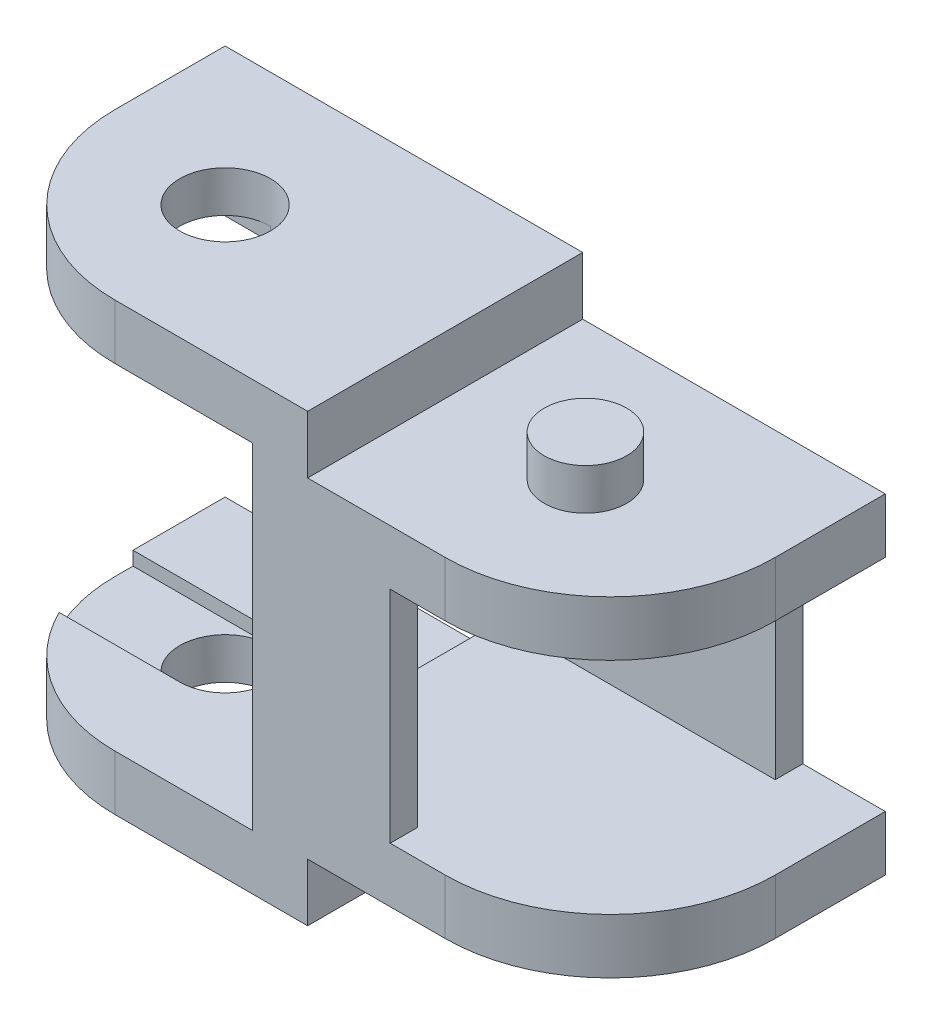
SolidWorks part; units mm, degrees
material "Сталь 45 ГОСТ 1050-2013"
ref_plane "Спереди" through (0, 0, 0) normal (0, 0, 1) x (1, 0, 0)
ref_plane "Сверху" through (0, 0, 0) normal (0, 1, 0) x (1, 0, 0)
ref_plane "Справа" through (0, 0, 0) normal (1, 0, 0) x (0, 0, -1)
sketch "Эскиз2" plane through (0, 0, 0) normal (0, 0, 1) x (1, 0, 0)
  line L0 (0, 0) -> (0, 2)
  line L1 (0, 2) -> (13, 2)
  line L2 (13, 2) -> (13, -0.1)
  line L3 (13, -0.1) -> (24, -0.1)
  line L4 (24, -0.1) -> (24, -2.1)
  line L5 (24, -2.1) -> (11, -2.1)
  line L6 (11, -2.1) -> (11, 0)
  line L7 (11, 0) -> (0, 0)
  point P3 (11, -2.0413)
  point P10 (0, 0)
  point P11 (0, 0)
  point P12 (0, 0)
  point P13 (13, -0.3101)
  dimension "D1" = 2
  dimension "D2" = 24
  dimension "D3" = 2
  dimension "D4" = 11
  dimension "D5" = 0.1
  dimension "D6" = 2
extrude "Бобышка-Вытянуть2" add sketch "Эскиз2" along normal blind 10
sketch "Эскиз3" plane through (0, -0.1, 0) normal (0, 1, 0) x (1, 0, 0)
  line L0 (0, -10) -> (0, 0) construction
  line L1 (24, -10) -> (24, 0) construction
  circle A0 centre (6, -5) radius 1.5 construction
  circle A1 centre (18.1, -5) radius 1.5
  point P4 (0, 0)
  point P5 (0, -5)
  dimension "D1" = 3
  dimension "D2" = 5.9
  dimension "D3" = 6
extrude "Бобышка-Вытянуть3" add sketch "Эскиз3" along normal blind 1.5
sketch "Эскиз5" plane through (0, 0, 0) normal (0, -1, 0) x (1, 0, 0)
  line L0 (0, 10) -> (0, 0) construction
  circle A0 centre (5, 5) radius 1.65
  point P2 (0, 5)
  point P3 (0, 0)
  dimension "D1" = 3.3
  dimension "D2" = 5
extrude "Вырез-Вытянуть2" cut sketch "Эскиз5" against normal through all
fillet "Скругление1" radius 6 2 edges at (24, -1.1, 10) (0, 1, 10)
sketch "Эскиз6" plane through (0, -2.1, 0) normal (0, -1, 0) x (-1, 0, 0)
  line L1 (-11, 0) -> (-21, 0)
  line L2 (-11, 0) -> (-11, -1)
  line L3 (-11, -1) -> (-21, -1)
  line L4 (-21, 0) -> (-21, -1)
  line L5 (-11, 0) -> (-21, -1) construction
  line L6 (-11, -1) -> (-21, 0) construction
  line L7 (-11, -9) -> (-16, -9)
  line L8 (-11, -9) -> (-11, -10)
  line L9 (-11, -10) -> (-16, -10)
  line L10 (-16, -9) -> (-16, -10)
  line L11 (-11, -9) -> (-16, -10) construction
  line L12 (-11, -10) -> (-16, -9) construction
  point P0 (-16, -0.5)
  point P5 (-13.5, -9.5)
  point P10 (-11, -10)
  point P12 (-11, 0)
  dimension "D1" = 1
  dimension "D2" = 10
  dimension "D3" = 5
extrude "Бобышка-Вытянуть4" add sketch "Эскиз6" along normal blind 4
sketch "Эскиз7" plane through (0, 0, 0) normal (0, -1, 0) x (1, 0, 0)
  line L1 (-0.6896, 3.35) -> (5, 3.35)
  line L2 (-0.6896, 3.35) -> (-0.6896, 6.65)
  line L3 (-0.6896, 6.65) -> (5, 6.65)
  line L4 (5, 3.35) -> (5, 6.65)
  line L5 (-0.6896, 3.35) -> (5, 6.65) construction
  line L6 (-0.6896, 6.65) -> (5, 3.35) construction
  circle A0 centre (5, 5) radius 1.65 construction
  point P0 (2.1552, 5)
  point P7 (5, 3.5)
extrude "Вырез-Вытянуть3" cut sketch "Эскиз7" against normal blind 0.5
mirror "Зеркальное отражение1" about plane through (0, -6.1, 0) normal (0, 1, 0) of bodies 111 109
